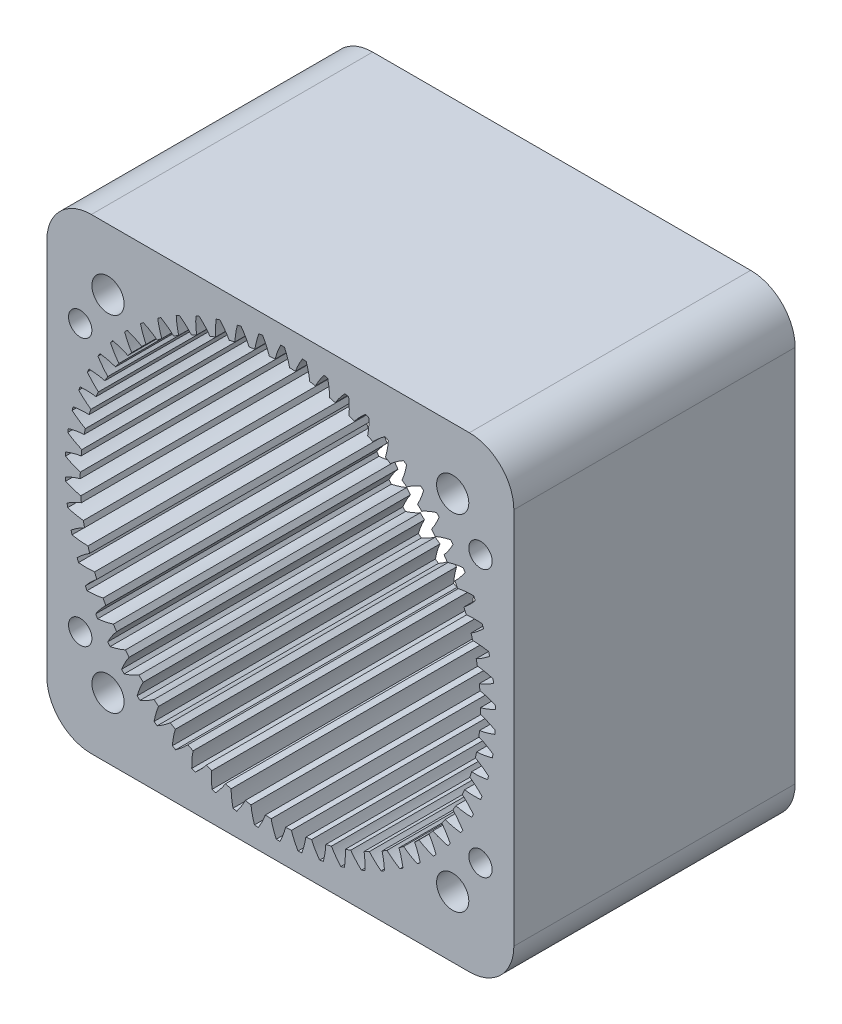
SolidWorks part; units mm, degrees
other "标注1"
sketch "草图9" plane through (-21, -21, 36) normal (-0.2153, -0.0648, 0.9744) x (0.3119, -0.9501, 0.0057)
other "标注2"
sketch "草图20" plane through (-30, -30, 20) normal (-0.0347, -0.0183, 0.9992) x (0.9994, -0.0065, 0.0346)
other "标注3"
sketch "草图27" plane through (-23.5298, 22.2328, 18) normal (-0.0197, 0.0107, 0.9997) x (0.9998, 0.0061, 0.0196)
ref_plane "前视基准面" through (0, 0, 0) normal (0, 0, 1) x (1, 0, 0)
ref_plane "上视基准面" through (0, 0, 0) normal (0, 1, 0) x (1, 0, 0)
ref_plane "右视基准面" through (0, 0, 0) normal (1, 0, 0) x (0, 0, -1)
sketch "草图1" plane through (0, 0, 0) normal (0, 0, 1) x (1, 0, 0)
  line L5 (-17.2128, -17.2128) -> (24.7872, 24.7872) construction
  line L6 (-21, 21) -> (21, -21) construction
  line L7 (21, 21) -> (-21, 21)
  line L8 (21, 21) -> (21, -21)
  line L9 (21, -21) -> (-21, -21)
  line L10 (-21, 21) -> (-21, -21)
  line L11 (0, -21) -> (0, 21) construction
  line L12 (21, 0) -> (-21, 0) construction
  circle A9 centre (0, 0) radius 30 construction
  circle A30 centre (15.5, 15.5) radius 1.55 construction
  circle A31 centre (15.5, -15.5) radius 1.55 construction
  circle A32 centre (-15.5, -15.5) radius 1.55 construction
  circle A33 centre (-15.5, 15.5) radius 1.55 construction
  point P31 (0, 0)
  point P37 (0, 0)
  point P48 (0, 0)
  dimension "D1" = 42
  dimension "D4" = 60
  dimension "D6" = 42
  dimension "D2" = 15.5
  dimension "D3" = 15.5
  dimension "D9" = 3.1
  dimension "D10" = 4
extrude "凸台-拉伸1" add sketch "草图1" along normal blind 25.3 contours L7 L10 L9 L8 A33 A32 A31 A30
sketch "草图6" plane through (0, 0, 0) normal (0, 0, 1) x (1, 0, 0)
  line L0 (0, 0) -> (17.4783, 0) construction
  line L1 (0, 0) -> (35.0568, 1.4114) construction
  line L2 (0, 0) -> (18.5979, 0.2772) construction
  circle A0 centre (0, 0) radius 18.6 construction
  circle A1 centre (0, 0) radius 5 construction
  circle A2 centre (0, 0) radius 17.4783 construction
  circle A3 centre (0, 0) radius 19.35 construction
  arc A4 (18.3136, -3.2516) -> (18.5979, 0.2772) centre (0, 0) cw construction
  circle A5 centre (0, 0) radius 10
  circle A7 centre (0, 0) radius 18
  arc A8 (19.3266, 0.951) -> (19.3404, 0.6105) centre (0, 0) cw
  spline S0 degree 4 poles (17.4783, 0) (17.4925, 0.0003) (17.5322, 0.0022) (17.607, 0.0095) (17.7287, 0.0269) (17.9531, 0.0708) (18.219, 0.1425) (18.5148, 0.2419) (18.8271, 0.3668) (19.0904, 0.4849) (19.3492, 0.6127) (19.6033, 0.7493) (19.9061, 0.9251) (20.2627, 1.1511) (20.668, 1.4349) (21.1151, 1.7826) (21.5533, 2.1589) (21.9735, 2.5535) (22.3775, 2.9674) (22.7628, 3.3942) (23.1343, 3.8408) (23.4399, 4.2347) (23.6995, 4.5935) (23.8967, 4.8761) (24.0713, 5.1411) (24.2387, 5.3961) (24.5035, 5.8331) (24.6633, 6.1083) (24.9023, 6.5423) (24.9838, 6.7039) (25.0508, 6.8322) knots 0 0 0 0 0 0.005377 0.015084 0.028532 0.04661 0.092111 0.119476 0.146842 0.174209 0.201575 0.228941 0.256307 0.307035 0.361767 0.4165 0.471232 0.525964 0.580697 0.635429 0.690161 0.744894 0.77226 0.799626 0.826992 0.854358 0.909091 0.954545 1 1 1 1 1 construction
  spline S1 degree 4 poles (17.4783, 0) (17.4925, 0.0003) (17.5322, 0.0022) (17.607, 0.0095) (17.7287, 0.0269) (17.9531, 0.0708) (18.219, 0.1425) (18.5148, 0.2419) (18.8271, 0.3668) (19.0904, 0.4849) (19.3492, 0.6127) (19.6033, 0.7493) (19.9061, 0.9251) (20.2627, 1.1511) (20.668, 1.4349) (21.1151, 1.7826) (21.5533, 2.1589) (21.9735, 2.5535) (22.3775, 2.9674) (22.7628, 3.3942) (23.1343, 3.8408) (23.4399, 4.2347) (23.6995, 4.5935) (23.8967, 4.8761) (24.0713, 5.1411) (24.2387, 5.3961) (24.4258, 5.7049) (24.5246, 5.8715) (24.5902, 5.985) knots 0 0 0 0 0 0.005377 0.015084 0.028532 0.04661 0.092111 0.119476 0.146842 0.174209 0.201575 0.228941 0.256307 0.307035 0.361767 0.4165 0.471232 0.525964 0.580697 0.635429 0.690161 0.744894 0.77226 0.799626 0.826992 0.854358 0.909091 0.909091 0.909091 0.909091 0.909091
  spline S2 degree 4 poles (17.2013, 1.4625) (17.2171, 1.4634) (17.2615, 1.4649) (17.3455, 1.4635) (17.4824, 1.4551) (17.7362, 1.4264) (18.0386, 1.3704) (18.3767, 1.2863) (18.7356, 1.1753) (19.0393, 1.0676) (19.3387, 0.9485) (19.6338, 0.8192) (19.9867, 0.6508) (20.4039, 0.4312) (20.8804, 0.1518) (21.4093, -0.1951) (21.9308, -0.5747) (22.4339, -0.9761) (22.9208, -1.4006) (23.388, -1.841) (23.8416, -2.3047) (24.2171, -2.7157) (24.5382, -3.0918) (24.7831, -3.3886) (25.0013, -3.6679) (25.2104, -3.9367) (25.4464, -4.2636) (25.5714, -4.4402) (25.6545, -4.5607) knots 0 0 0 0 0 0.005377 0.015084 0.028532 0.04661 0.092111 0.119476 0.146842 0.174209 0.201575 0.228941 0.256307 0.307035 0.361767 0.4165 0.471232 0.525964 0.580697 0.635429 0.690161 0.744894 0.77226 0.799626 0.826992 0.854358 0.909091 0.909091 0.909091 0.909091 0.909091
  point P6 (30.6834, 1.2647)
  dimension "D1" = 37.2
  dimension "D2" = 10
  dimension "D3" = 38.7
  dimension "D4" = 34.9566
  dimension "D6" = 36
  dimension "D7" = 20
  dimension "D5" = 1.452
extrude "切除-拉伸1" cut sketch "草图6" along normal through all
pattern_circular "阵列(圆周)1" count 62 over 360 about axis through (0, 0, 0) along (0, 0, -1) of "切除-拉伸1"
fillet "圆角2" radius 4 4 edges at (21, -21, 12.65) (-21, -21, 12.65) (-21, 21, 12.65) (21, 21, 12.65)
sketch "草图23" plane through (0, 0, 0) normal (0, 0, -1) x (-1, 0, 0)
  line L0 (-21, 17) -> (-21, -17) construction
  line L1 (-21, 13) -> (-17, 13)
  line L2 (-21, 13) -> (-21, 9)
  line L5 (-17, 21) -> (17, 21) construction
  line L18 (-21, 9) -> (-17, 13)
  line L19 (9, 21) -> (13, 17)
  line L20 (13, 21) -> (13, 17)
  line L21 (13, 21) -> (9, 21)
  line L22 (21, -9) -> (17, -13)
  line L23 (21, -13) -> (17, -13)
  line L24 (21, -13) -> (21, -9)
  line L25 (-9, -21) -> (-13, -17)
  line L26 (-13, -21) -> (-13, -17)
  line L27 (-13, -21) -> (-9, -21)
  point P19 (0, 0)
  point P23 (-7, 0)
  dimension "D1" = 4
  dimension "D2" = 4
  dimension "D3" = 8
  dimension "D4" = 4
extrude "切除-拉伸14" [suppressed] cut sketch "草图23" against normal blind 3
sketch "草图24" plane through (0, 0, 25.3) normal (0, 0, 1) x (1, 0, 0)
  line L0 (-21, 13) -> (-17, 13)
  line L1 (-21, 13) -> (-21, 9)
  line L16 (-21, 17) -> (-21, -17) construction
  line L17 (17, 21) -> (-17, 21) construction
  line L30 (-21, 9) -> (-17, 13)
  line L40 (9, 21) -> (13, 17)
  line L41 (13, 21) -> (13, 17)
  line L42 (13, 21) -> (9, 21)
  line L43 (21, -9) -> (17, -13)
  line L44 (21, -13) -> (17, -13)
  line L45 (21, -13) -> (21, -9)
  line L46 (-9, -21) -> (-13, -17)
  line L47 (-13, -21) -> (-13, -17)
  line L48 (-13, -21) -> (-9, -21)
  point P16 (0.2043, -0.1277)
  point P20 (0.2043, -0.1277)
  point P21 (0, 0)
  point P24 (-7, 0)
  dimension "D1" = 4
  dimension "D2" = 4
  dimension "D3" = 8
  dimension "D4" = 4
extrude "切除-拉伸15" [suppressed] cut sketch "草图24" against normal blind 4
sketch "草图25" plane through (0, 0, 25.3) normal (0, 0, 1) x (1, 0, 0)
  line L0 (17, 21) -> (-17, 21) construction
  line L1 (-21, 17) -> (-21, -17) construction
  line L2 (0, 22.2328) -> (0, -23.0812) construction
  line L3 (-23.5298, 0) -> (36.1925, 0) construction
  circle A0 centre (-18, 12) radius 1.05
  circle A1 centre (18, 12) radius 1.05
  circle A2 centre (18, -12) radius 1.05
  circle A3 centre (-18, -12) radius 1.05
  dimension "D1" = 2.1
  dimension "D2" = 9
  dimension "D3" = 3
extrude "切除-拉伸16" cut sketch "草图25" against normal through all
sketch "草图28" plane through (0, 0, 25.3) normal (0, 0, 1) x (1, 0, 0)
  line L0 (-23.5298, 0) -> (36.1925, 0) construction
  line L1 (0, 22.2328) -> (0, -23.0812) construction
  circle A0 centre (-15.5, 15.5) radius 1.45
  circle A1 centre (15.5, 15.5) radius 1.45
  circle A2 centre (15.5, -15.5) radius 1.45
  circle A3 centre (-15.5, -15.5) radius 1.45
  point P15 (0, 0)
  dimension "D1" = 2.9
  dimension "D2" = 15.5
  dimension "D3" = 15.5
  dimension "D4" = 4
extrude "切除-拉伸17" cut sketch "草图28" against normal blind 8
sketch "草图29" plane through (0, 0, 0) normal (0, 0, -1) x (-1, 0, 0)
  line L2 (-16.9706, 16.9706) -> (0, 0) construction
  line L3 (0, 22.2328) -> (0, -23.0812) construction
  circle A0 centre (-16.9706, 16.9706) radius 2.1
  circle A1 centre (16.9706, 16.9706) radius 2.1
  circle A2 centre (16.9706, -16.9706) radius 2.1
  circle A3 centre (-16.9706, -16.9706) radius 2.1
  point P12 (0, 0)
  dimension "D4" = 4.2
  dimension "D1" = 24
  dimension "D3" = 45
  dimension "D2" = 4
extrude "切除-拉伸18" cut sketch "草图29" against normal blind 8
equation "\"m\"= 0.6"
equation "\"z\"= 62"
equation "\"a\"= 20"
equation "\"d\"= \"m\" * \"z\""
equation "\"da\"= \"m\" * ( \"z\" - 2 )"
equation "\"df\"= \"d\" + 2.5 * \"m\""
equation "\"db\"= \"d\" * cos ( \"a\" )"
equation "\"s\"= pi * \"m\" / 2"
equation "\"D1@草图6\"=\"d\""
equation "\"D3@草图6\"=\"df\""
equation "\"D4@草图6\"=\"db\""
equation "\"D6@草图6\"=\"da\""
equation "\"sr\"= 360 / \"z\" / 4"
equation "\"D5@草图6\"=\"sr\""
equation "\"D1@阵列(圆周)1\"=\"z\""
